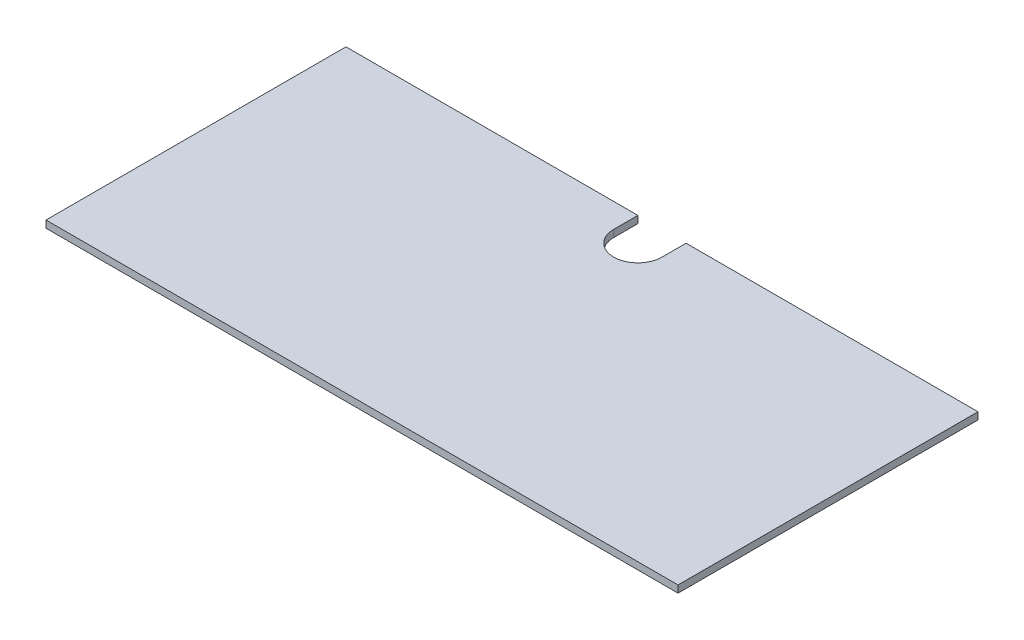
SolidWorks part; units mm, degrees
ref_plane "Front Plane" through (0, 0, 0) normal (0, 0, 1) x (1, 0, 0)
ref_plane "Top Plane" through (0, 0, 0) normal (0, 1, 0) x (1, 0, 0)
ref_plane "Right Plane" through (0, 0, 0) normal (1, 0, 0) x (0, 0, -1)
sketch "Sketch2" plane through (0, 0, 0) normal (0, 1, 0) x (1, 0, 0)
  line L0 (302.4187, 266.7) -> (561.975, 266.7)
  line L1 (0, 0) -> (561.975, 0)
  line L2 (0, 0) -> (0, 266.7)
  line L3 (0, 266.7) -> (259.5562, 266.7)
  line L4 (561.975, 0) -> (561.975, 266.7)
  line L5 (280.9875, 315.1209) -> (280.9875, -60.24) construction
  line L6 (259.5562, 266.7) -> (259.5563, 245.2688)
  line L8 (302.4187, 266.7) -> (302.4187, 245.2687)
  arc A0 (259.5563, 245.2688) -> (302.4187, 245.2687) centre (280.9875, 245.2688) ccw
  point P10 (280.9875, 223.8375)
  dimension "D1" = 561.975
  dimension "D2" = 266.7
  dimension "D3" = 42.8625
  dimension "D4" = 42.8625
  dimension "D5" = 280.9875
extrude "Boss-Extrude1" add sketch "Sketch2" along normal blind 6.35
ref_plane "Plane1" through (280.9875, 0, 0) normal (-1, 0, 0) x (0, 0, 1)
